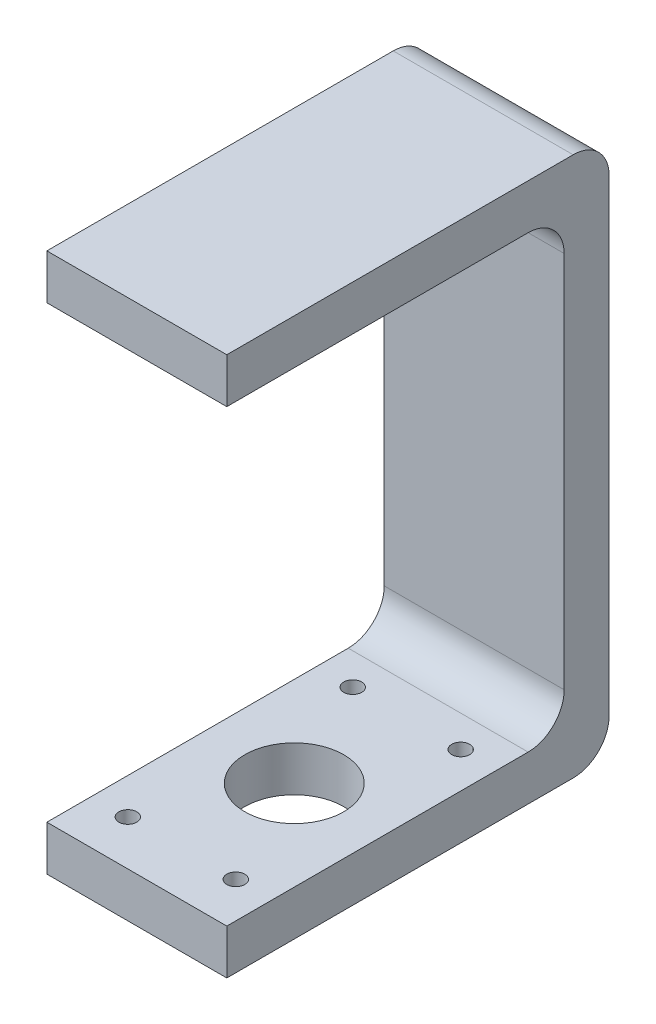
SolidWorks part; units mm, degrees
material "普通碳钢"
ref_plane "前视基准面" through (0, 0, 0) normal (0, 0, 1) x (1, 0, 0)
ref_plane "上视基准面" through (0, 0, 0) normal (0, 1, 0) x (1, 0, 0)
ref_plane "右视基准面" through (0, 0, 0) normal (1, 0, 0) x (0, 0, -1)
sketch "草图1" plane through (0, 0, 0) normal (1, 0, 0) x (0, 0, -1)
  line L0 (0, 0) -> (77, 0)
  line L1 (85, 8) -> (85, 112)
  line L2 (77, 120) -> (0, 120)
  line L3 (0, 120) -> (0, 110)
  line L4 (0, 110) -> (67, 110)
  line L5 (75, 102) -> (75, 18)
  line L6 (67, 10) -> (0, 10)
  line L7 (0, 10) -> (0, 0)
  arc A0 (67, 10) -> (75, 18) centre (67, 18) ccw
  arc A1 (75, 102) -> (67, 110) centre (67, 102) ccw
  arc A2 (85, 8) -> (77, 0) centre (77, 8) cw
  arc A3 (85, 112) -> (77, 120) centre (77, 112) ccw
  point P11 (75, 10)
  point P14 (75, 110)
  point P17 (85, 0)
  point P20 (85, 120)
  dimension "D7" = 8
  dimension "D1" = 85
  dimension "D2" = 75
  dimension "D3" = 10
  dimension "D5" = 100
  dimension "D6" = 10
extrude "凸台-拉伸1" add sketch "草图1" along normal blind 40
sketch "草图5" plane through (0, 0, 0) normal (0, -1, 0) x (1, 0, 0)
  line L0 (20, 0) -> (20, -70) construction
  line L1 (40, 0) -> (0, 0) construction
  circle A0 centre (20, -35) radius 11
  circle A1 centre (20, -35) radius 28 construction
  dimension "D1" = 22
  dimension "D3" = 56
  dimension "D2" = 35
extrude "切除-拉伸1" cut sketch "草图5" against normal up to next
sketch "草图6" plane through (0, 0, 0) normal (0, -1, 0) x (1, 0, 0)
  circle A0 centre (8, -10) radius 2 construction
  circle A1 centre (32, -10) radius 2 construction
  circle A2 centre (8, -60) radius 2 construction
  circle A3 centre (32, -60) radius 2 construction
  circle A4 centre (8, -10) radius 2
  circle A5 centre (32, -10) radius 2
  circle A6 centre (8, -60) radius 2
  circle A7 centre (32, -60) radius 2
extrude "切除-拉伸2" cut sketch "草图6" against normal blind 20
